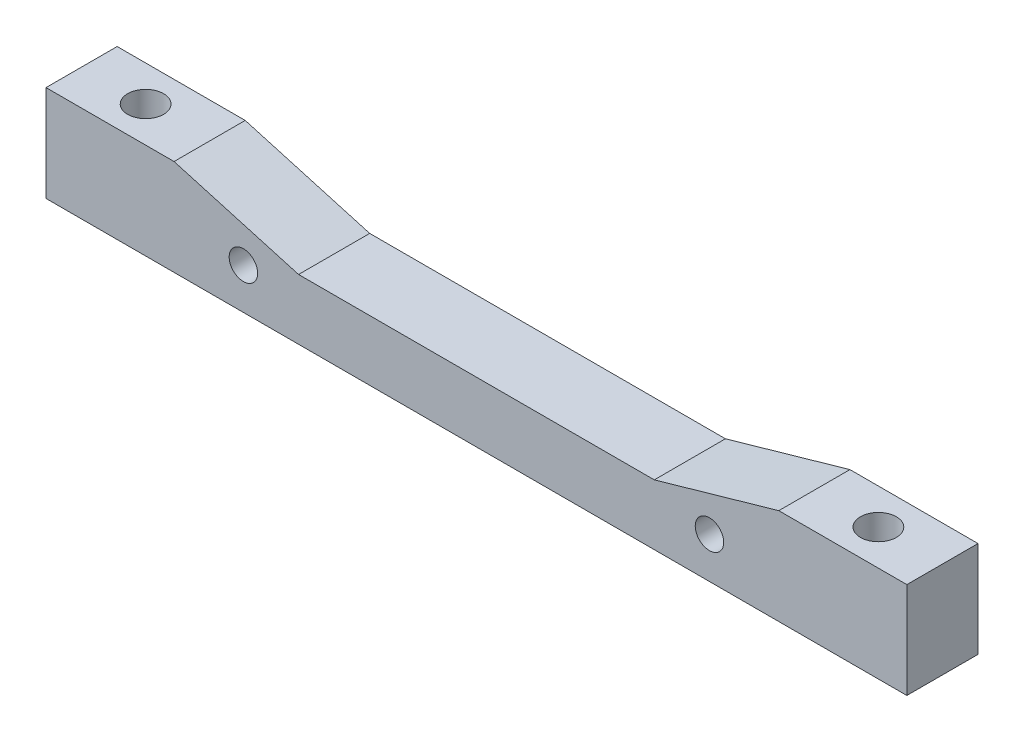
SolidWorks part; units mm, degrees
ref_plane "Alzado" through (0, 0, 0) normal (0, 0, 1) x (1, 0, 0)
ref_plane "Planta" through (0, 0, 0) normal (0, 1, 0) x (1, 0, 0)
ref_plane "Vista lateral" through (0, 0, 0) normal (1, 0, 0) x (0, 0, -1)
sketch "Croquis1" plane through (0, 0, 0) normal (0, 1, 0) x (1, 0, 0)
  line L1 (0, 0) -> (121, 0)
  line L2 (0, 0) -> (0, 10)
  line L3 (0, 10) -> (121, 10)
  line L4 (121, 0) -> (121, 10)
  dimension "D1" = 121
  dimension "D2" = 10
extrude "Saliente-Extruir1" add sketch "Croquis1" along normal blind 13.5
sketch "Croquis2" plane through (0, 13.5, 0) normal (0, 1, 0) x (1, 0, 0)
  line L0 (0, 5) -> (6, 5) construction
  line L1 (0, 10) -> (0, 0) construction
  line L2 (6, 5) -> (9, 5) construction
  line L3 (60.5, 10) -> (60.5, 0) construction
  line L4 (121, 10) -> (0, 10) construction
  line L5 (0, 0) -> (121, 0) construction
  circle A0 centre (9, 5) radius 2.525
  circle A1 centre (112, 5) radius 2.525
  dimension "D1" = 9
  dimension "D2" = 5.05
extrude "Cortar-Extruir1" cut sketch "Croquis2" against normal blind 8.05
sketch "Croquis3" plane through (0, 0, 0) normal (0, 0, 1) x (1, 0, 0)
  line L0 (60.5, 13.5) -> (60.5, 0) construction
  line L1 (0, 13.5) -> (121, 13.5) construction
  line L2 (0, 0) -> (121, 0) construction
  line L3 (103, 13.5) -> (18, 13.5)
  line L4 (85.5, 8.5) -> (35.5, 8.5)
  line L5 (35.5, 8.5) -> (121, 8.5) construction
  line L6 (121, 13.5) -> (121, 0) construction
  line L7 (18, 13.5) -> (35.5, 8.5)
  line L8 (103, 13.5) -> (85.5, 8.5)
  point P11 (60.5, 8.5)
  point P15 (60.5, 8.5)
  dimension "D1" = 5
extrude "Cortar-Extruir2" cut sketch "Croquis3" against normal blind 20
sketch "Croquis4" plane through (0, 0, 0) normal (0, 0, 1) x (1, 0, 0)
  line L0 (60.5, 8.5) -> (60.5, 0) construction
  line L1 (35.5, 8.5) -> (85.5, 8.5) construction
  line L2 (0, 0) -> (121, 0) construction
  line L3 (23.75, 0) -> (23.75, 5.76) construction
  line L4 (23.75, 5.76) -> (60.5, 5.76) construction
  line L5 (60.5, 5.76) -> (27.745, 5.76) construction
  circle A0 centre (27.745, 5.76) radius 2
  circle A1 centre (93.255, 5.76) radius 2
  dimension "D1" = 5.76
  dimension "D3" = 4
  dimension "D2" = 32.755
extrude "Cortar-Extruir3" cut sketch "Croquis4" against normal blind 20
